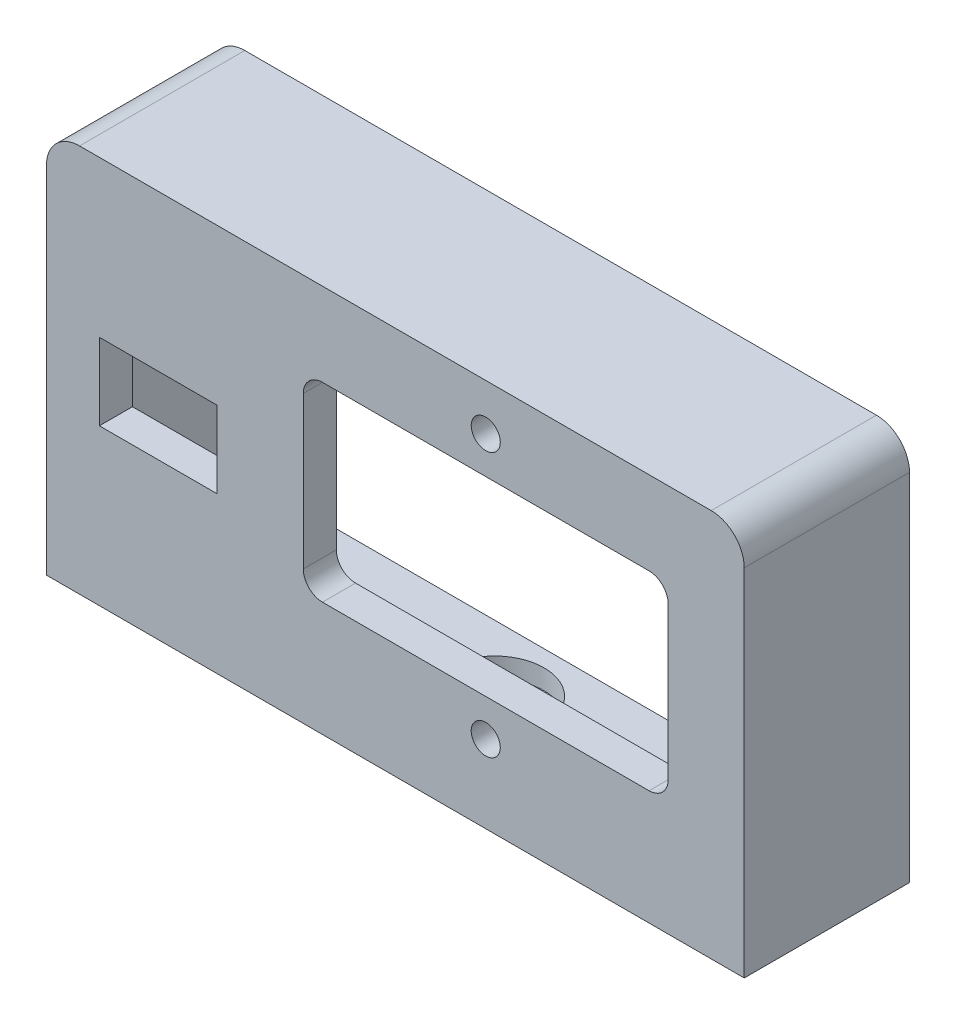
SolidWorks part; units mm, degrees
ref_plane "Front Plane" through (0, 0, 0) normal (0, 0, 1) x (1, 0, 0)
ref_plane "Top Plane" through (0, 0, 0) normal (0, 1, 0) x (1, 0, 0)
ref_plane "Right Plane" through (0, 0, 0) normal (1, 0, 0) x (0, 0, -1)
sketch "Esboço1" plane through (0, 0, 0) normal (0, 0, 1) x (1, 0, 0)
  line L1 (-47.8682, -30.8259) -> (57.6762, -30.8259)
  line L2 (-47.8682, -30.8259) -> (-47.8682, -89.5621)
  line L3 (-47.8682, -89.5621) -> (57.6762, -89.5621)
  line L4 (57.6762, -30.8259) -> (57.6762, -89.5621)
  line L25 (43.2762, -43.4259) -> (-6.1238, -43.4259)
  line L26 (46.1762, -69.3259) -> (46.1762, -46.3259)
  line L27 (-6.1238, -72.2259) -> (43.2762, -72.2259)
  line L28 (-9.0238, -46.3259) -> (-9.0238, -69.3259)
  circle A13 centre (18.5762, -37.8259) radius 2.2
  arc A18 (-6.1238, -43.4259) -> (-9.0238, -46.3259) centre (-6.1238, -46.3259) ccw
  arc A19 (46.1762, -46.3259) -> (43.2762, -43.4259) centre (43.2762, -46.3259) ccw
  arc A20 (43.2762, -72.2259) -> (46.1762, -69.3259) centre (43.2762, -69.3259) ccw
  arc A21 (-9.0238, -69.3259) -> (-6.1238, -72.2259) centre (-6.1238, -69.3259) ccw
  circle A24 centre (18.5762, -77.8259) radius 2.2
extrude "Ressalto-extrusão1" add sketch "Esboço1" along normal blind 5
sketch "Esboço2" plane through (0, 0, 5) normal (0, 0, 1) x (1, 0, 0)
  line L0 (-47.8682, -60.194) -> (-31.8682, -60.194) construction
  line L1 (-47.8682, -30.8259) -> (-47.8682, -89.5621) construction
  line L7 (-39.8682, -54.394) -> (-22.0682, -54.394)
  line L8 (-39.8682, -54.394) -> (-39.8682, -65.994)
  line L9 (-39.8682, -65.994) -> (-22.0682, -65.994)
  line L10 (-22.0682, -54.394) -> (-22.0682, -65.994)
  point P10 (-39.8682, -60.194)
  dimension "D1" = 8
  dimension "D2" = 17.8
  dimension "D3" = 11.6
extrude "Corte-extrusão1" cut sketch "Esboço2" against normal blind 10
fillet "Filete1" radius 5 2 edges at (57.6762, -30.8259, 2.5) (-47.8682, -30.8259, 2.5)
sketch "Esboço3" plane through (0, 0, 0) normal (0, 0, -1) x (-1, 0, 0)
  line L0 (42.8682, -33.8259) -> (-52.6762, -33.8259)
  line L1 (-54.6762, -35.8259) -> (-54.6762, -86.5621)
  line L2 (-54.6762, -86.5621) -> (44.8682, -86.5621)
  line L3 (44.8682, -86.5621) -> (44.8682, -35.8259)
  line L8 (42.8682, -30.8259) -> (-52.6762, -30.8259)
  line L9 (-57.6762, -35.8259) -> (-57.6762, -89.5621)
  line L10 (-57.6762, -89.5621) -> (47.8682, -89.5621)
  line L11 (47.8682, -89.5621) -> (47.8682, -35.8259)
  line L12 (42.8682, -30.8259) -> (-52.6762, -30.8259)
  line L13 (-57.6762, -35.8259) -> (-57.6762, -89.5621)
  line L14 (-57.6762, -89.5621) -> (47.8682, -89.5621)
  line L15 (47.8682, -89.5621) -> (47.8682, -35.8259)
  arc A0 (-52.6762, -33.8259) -> (-54.6762, -35.8259) centre (-52.6762, -35.8259) ccw
  arc A1 (44.8682, -35.8259) -> (42.8682, -33.8259) centre (42.8682, -35.8259) ccw
  arc A4 (-52.6762, -30.8259) -> (-57.6762, -35.8259) centre (-52.6762, -35.8259) ccw
  arc A5 (47.8682, -35.8259) -> (42.8682, -30.8259) centre (42.8682, -35.8259) ccw
  arc A6 (-52.6762, -30.8259) -> (-57.6762, -35.8259) centre (-52.6762, -35.8259) ccw
  arc A7 (47.8682, -35.8259) -> (42.8682, -30.8259) centre (42.8682, -35.8259) ccw
  dimension "D1" = 0
  dimension "D2" = 3
extrude "Ressalto-extrusão2" add sketch "Esboço3" along normal blind 20
sketch "Esboço4" plane through (0, -86.5621, 0) normal (0, 1, 0) x (1, 0, 0)
  line L0 (-44.8682, 10) -> (54.6762, 10) construction
  line L1 (-44.8682, 20) -> (-44.8682, 0) construction
  line L2 (54.6762, 20) -> (54.6762, 0) construction
  line L3 (29.6762, 0) -> (29.6762, 20) construction
  line L4 (54.6762, 0) -> (-44.8682, 0) construction
  line L5 (54.6762, 20) -> (-44.8682, 20) construction
  line L6 (-19.8682, 0) -> (-19.8682, 20) construction
  circle A0 centre (4.904, 10) radius 7.5
  point P17 (4.904, 10)
  dimension "D3" = 15
  dimension "D1" = 25
  dimension "D2" = 25
hole_wizard "Broca de rosquear para tarraxa de M3x0.51" positions "Esboço7" profile "Esboço8" hole size "M3x0.5" standard "Ansi Metric"
sketch "Esboço7" plane through (0, -86.5621, 0) normal (0, 1, 0) x (1, 0, 0)
  point P0 (29.6458, 10.0286)
  point P2 (-19.9137, 10.0286)
sketch "Esboço8" plane through (29.6458, -86.5621, -10.0286) normal (1, 0, 0) x (0, 0, 1)
  line L0 (0, 0) -> (0, 3)
  line L1 (0, 3) -> (1.25, 3)
  line L2 (1.25, 3) -> (1.25, 0)
  line L5 (1.25, 0) -> (0, 0)
  line L11 (0, -6.35) -> (0, 107.95) construction
  dimension "Thru Hole Dia." = 2.5
  dimension "Thru Hole Depth" = 3
extrude "Corte-extrusão2" cut sketch "Esboço4" against normal blind 10
